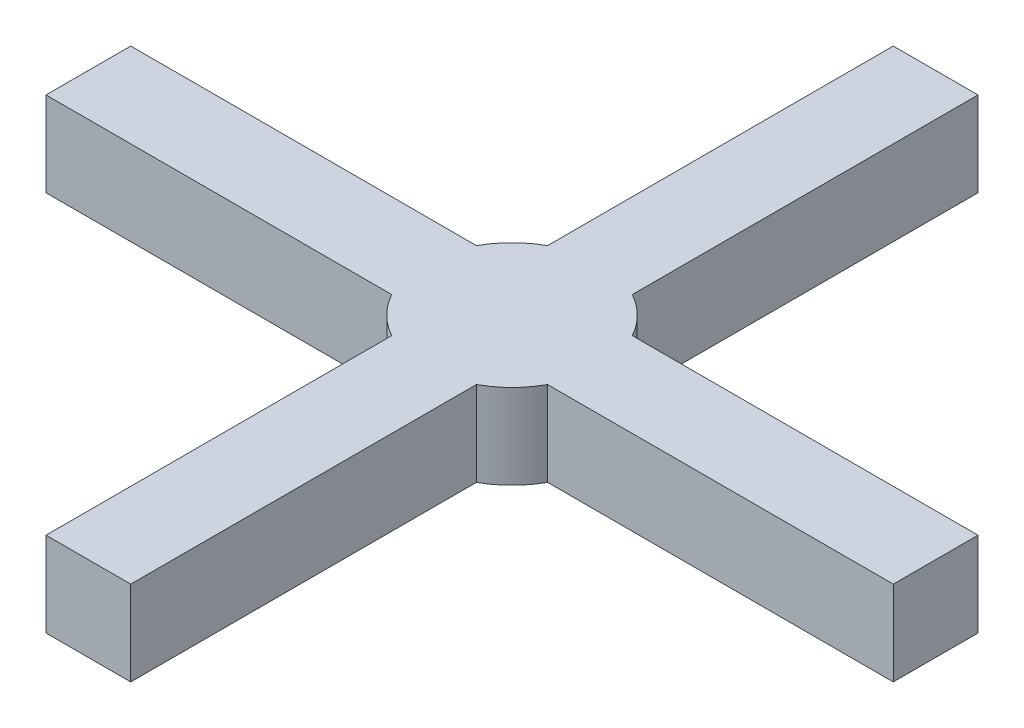
SolidWorks part; units mm, degrees
material "Plain Carbon Steel"
ref_plane "Front Plane" through (0, 0, 0) normal (0, 0, 1) x (1, 0, 0)
ref_plane "Top Plane" through (0, 0, 0) normal (0, 1, 0) x (1, 0, 0)
ref_plane "Right Plane" through (0, 0, 0) normal (1, 0, 0) x (0, 0, -1)
sketch "Sketch1" plane through (0, 0, 0) normal (0, 1, 0) x (1, 0, 0)
  line L0 (-152.4, -280.3598) -> (-152.4, -1524)
  line L1 (-152.4, 1524) -> (152.4, 1524)
  line L2 (-152.4, 1524) -> (-152.4, 280.3598)
  line L3 (-152.4, -1524) -> (152.4, -1524)
  line L4 (152.4, 1524) -> (152.4, 280.3598)
  line L6 (-15.24, -152.4) -> (0, 0) construction
  line L7 (-1524, 152.4) -> (-280.3598, 152.4)
  line L8 (-1524, 152.4) -> (-1524, -152.4)
  line L9 (-1524, -152.4) -> (-280.3598, -152.4)
  line L10 (1524, 152.4) -> (1524, -152.4)
  line L11 (-131.5042, 13.1504) -> (0, 0) construction
  line L12 (-1524, -152.4) -> (-317.5204, -31.752) construction
  line L13 (280.3598, 152.4) -> (1524, 152.4)
  line L15 (280.3598, -152.4) -> (1524, -152.4)
  line L18 (152.4, -280.3598) -> (152.4, -1524)
  arc A0 (-280.3598, -152.4) -> (-152.4, -280.3598) centre (0, 0) ccw
  arc A1 (152.4, -280.3598) -> (280.3598, -152.4) centre (0, 0) ccw
  arc A2 (280.3598, 152.4) -> (152.4, 280.3598) centre (0, 0) ccw
  arc A3 (-152.4, 280.3598) -> (-280.3598, 152.4) centre (0, 0) ccw
  point P0 (0, 0)
  point P6 (0, 0)
  dimension "D1" = 3048
  dimension "D2" = 3048
  dimension "D3" = 304.8
  dimension "D4" = 304.8
extrude "Boss-Extrude1" add sketch "Sketch1" against normal blind 304.8 from offset 5105.4
